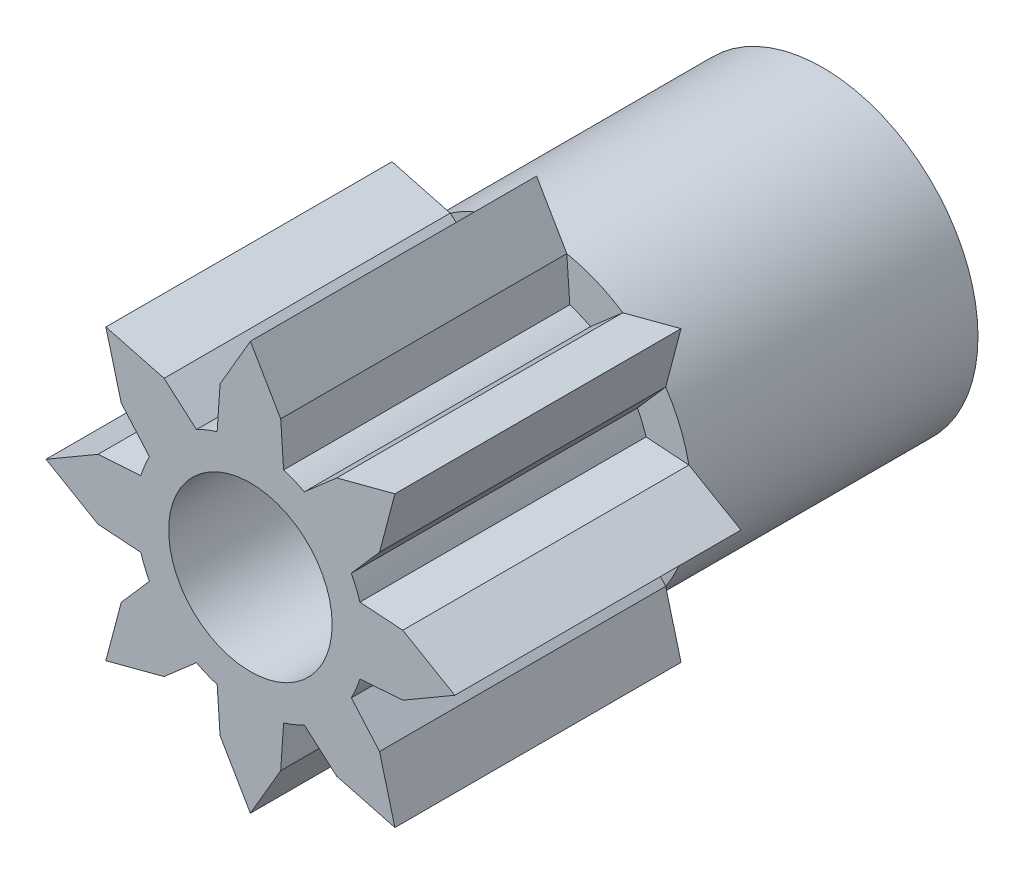
SolidWorks part; units mm, degrees
ref_plane "Front Plane" through (0, 0, 0) normal (0, 0, 1) x (1, 0, 0)
ref_plane "Top Plane" through (0, 0, 0) normal (0, 1, 0) x (1, 0, 0)
ref_plane "Right Plane" through (0, 0, 0) normal (1, 0, 0) x (0, 0, -1)
sketch "Sketch1" plane through (0, 0, 0) normal (0, 0, 1) x (1, 0, 0)
  circle A0 centre (0, 0) radius 1.9
  circle A1 centre (0, 0) radius 1
  circle A2 centre (0, 0) radius 1
  dimension "D2" = 3.8
  dimension "D1" = 0
extrude "Boss-Extrude1" add sketch "Sketch1" against normal blind 7
sketch "Sketch2" plane through (0, 0, 0) normal (0, 0, 1) x (1, 0, 0)
  circle A0 centre (0, 0) radius 1.9 construction
  circle A1 centre (0, 0) radius 1.4
  circle A2 centre (0, 0) radius 1.9
extrude "Cut-Extrude1" cut sketch "Sketch2" against normal blind 3.5
sketch "Sketch3" plane through (0, 0, 0) normal (0, 0, 1) x (1, 0, 0)
  line L0 (1.5798, 1.0556) -> (1.7678, 1.7678)
  line L1 (0.3707, 1.8635) -> (0, 2.5)
  line L2 (0.3707, 1.8635) -> (0.4064, 1.3397)
  line L3 (1.5798, 1.0556) -> (1.2347, 0.66)
  line L4 (-0.3707, 1.8635) -> (0, 2.5)
  line L5 (-0.3707, 1.8635) -> (-0.4064, 1.3397)
  line L6 (1.0556, 1.5798) -> (1.7678, 1.7678)
  line L7 (1.0556, 1.5798) -> (0.66, 1.2347)
  line L8 (1.8635, -0.3707) -> (2.5, 0)
  line L9 (1.8635, -0.3707) -> (1.3397, -0.4064)
  line L10 (1.8635, 0.3707) -> (2.5, 0)
  line L11 (1.8635, 0.3707) -> (1.3397, 0.4064)
  line L12 (1.0556, -1.5798) -> (1.7678, -1.7678)
  line L13 (1.0556, -1.5798) -> (0.66, -1.2347)
  line L14 (1.5798, -1.0556) -> (1.7678, -1.7678)
  line L15 (1.5798, -1.0556) -> (1.2347, -0.66)
  line L16 (-0.3707, -1.8635) -> (0, -2.5)
  line L17 (-0.3707, -1.8635) -> (-0.4064, -1.3397)
  line L18 (0.3707, -1.8635) -> (0, -2.5)
  line L19 (0.3707, -1.8635) -> (0.4064, -1.3397)
  line L20 (-1.5798, -1.0556) -> (-1.7678, -1.7678)
  line L21 (-1.5798, -1.0556) -> (-1.2347, -0.66)
  line L22 (-1.0556, -1.5798) -> (-1.7678, -1.7678)
  line L23 (-1.0556, -1.5798) -> (-0.66, -1.2347)
  line L24 (-1.8635, 0.3707) -> (-2.5, 0)
  line L25 (-1.8635, 0.3707) -> (-1.3397, 0.4064)
  line L26 (-1.8635, -0.3707) -> (-2.5, 0)
  line L27 (-1.8635, -0.3707) -> (-1.3397, -0.4064)
  line L28 (-1.0556, 1.5798) -> (-1.7678, 1.7678)
  line L29 (-1.0556, 1.5798) -> (-0.66, 1.2347)
  line L30 (-1.5798, 1.0556) -> (-1.7678, 1.7678)
  line L31 (-1.5798, 1.0556) -> (-1.2347, 0.66)
  arc A0 (0.4064, 1.3397) -> (0.5358, 1.2934) centre (0, 0) cw
  circle A1 centre (0, 0) radius 1.4 construction
  arc A2 (-0.4064, 1.3397) -> (-0.5358, 1.2934) centre (0, 0) ccw
  arc A3 (1.2347, 0.66) -> (1.2934, 0.5358) centre (0, 0) cw
  arc A4 (0.66, 1.2347) -> (0.5358, 1.2934) centre (0, 0) ccw
  arc A5 (1.3397, -0.4064) -> (1.2934, -0.5358) centre (0, 0) cw
  arc A6 (1.3397, 0.4064) -> (1.2934, 0.5358) centre (0, 0) ccw
  arc A7 (0.66, -1.2347) -> (0.5358, -1.2934) centre (0, 0) cw
  arc A8 (1.2347, -0.66) -> (1.2934, -0.5358) centre (0, 0) ccw
  arc A9 (-0.4064, -1.3397) -> (-0.5358, -1.2934) centre (0, 0) cw
  arc A10 (0.4064, -1.3397) -> (0.5358, -1.2934) centre (0, 0) ccw
  arc A11 (-1.2347, -0.66) -> (-1.2934, -0.5358) centre (0, 0) cw
  arc A12 (-0.66, -1.2347) -> (-0.5358, -1.2934) centre (0, 0) ccw
  arc A13 (-1.3397, 0.4064) -> (-1.2934, 0.5358) centre (0, 0) cw
  arc A14 (-1.3397, -0.4064) -> (-1.2934, -0.5358) centre (0, 0) ccw
  arc A15 (-0.66, 1.2347) -> (-0.5358, 1.2934) centre (0, 0) cw
  arc A16 (-1.2347, 0.66) -> (-1.2934, 0.5358) centre (0, 0) ccw
  circle A17 centre (0, 0) radius 1 construction
  circle A18 centre (0, 0) radius 1
  point P60 (0, 0)
  dimension "D1" = 8
extrude "Boss-Extrude2" add sketch "Sketch3" against normal up to surface (3.5 mm away) up to face at (1.4, 0, -3.5)
